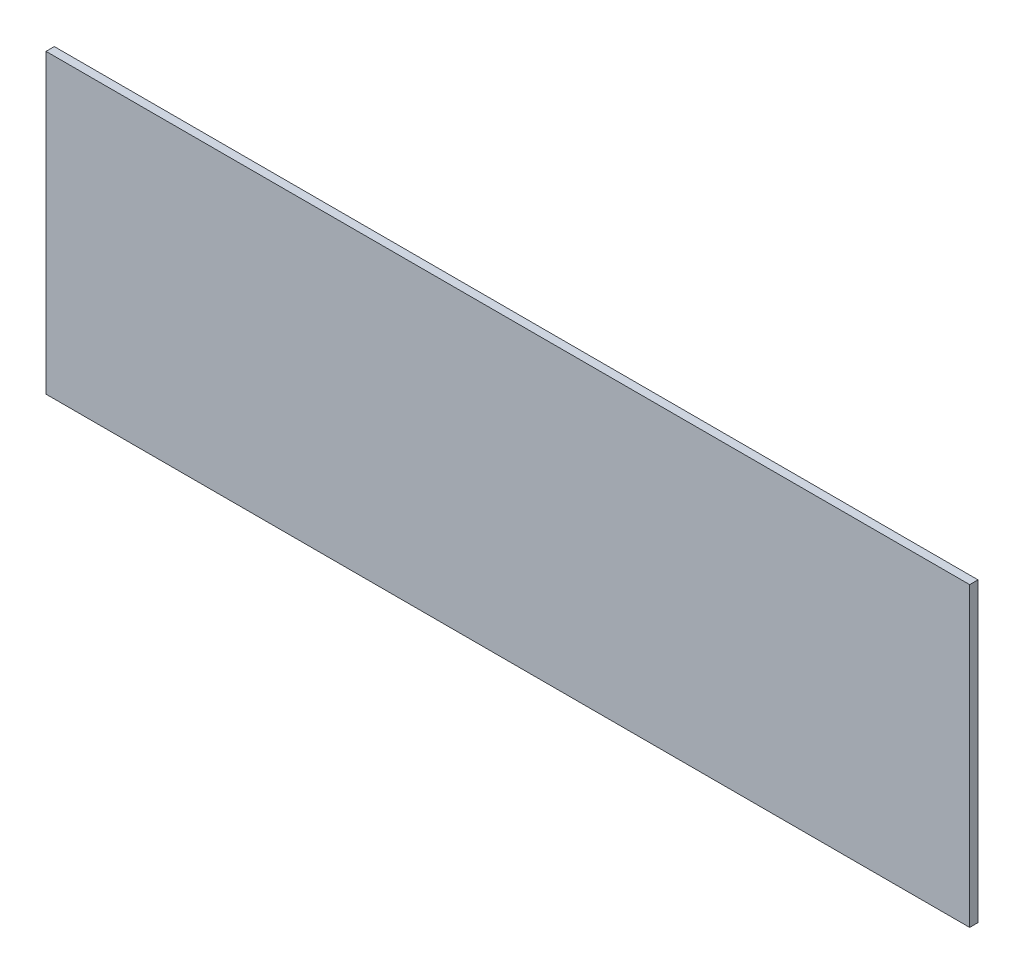
SolidWorks part; units mm, degrees
ref_plane "Front Plane" through (0, 0, 0) normal (0, 0, 1) x (1, 0, 0)
ref_plane "Top Plane" through (0, 0, 0) normal (0, 1, 0) x (1, 0, 0)
ref_plane "Right Plane" through (0, 0, 0) normal (1, 0, 0) x (0, 0, -1)
sketch "Sketch2" plane through (0, 0, 0) normal (0, 0, 1) x (1, 0, 0)
  line L1 (0, 0) -> (177.8, 0)
  line L2 (0, 0) -> (0, -57.15)
  line L3 (0, -57.15) -> (177.8, -57.15)
  line L4 (177.8, 0) -> (177.8, -57.15)
  dimension "D1" = 177.8
  dimension "D2" = 57.15
extrude "Boss-Extrude1" add sketch "Sketch2" along normal blind 1.6
